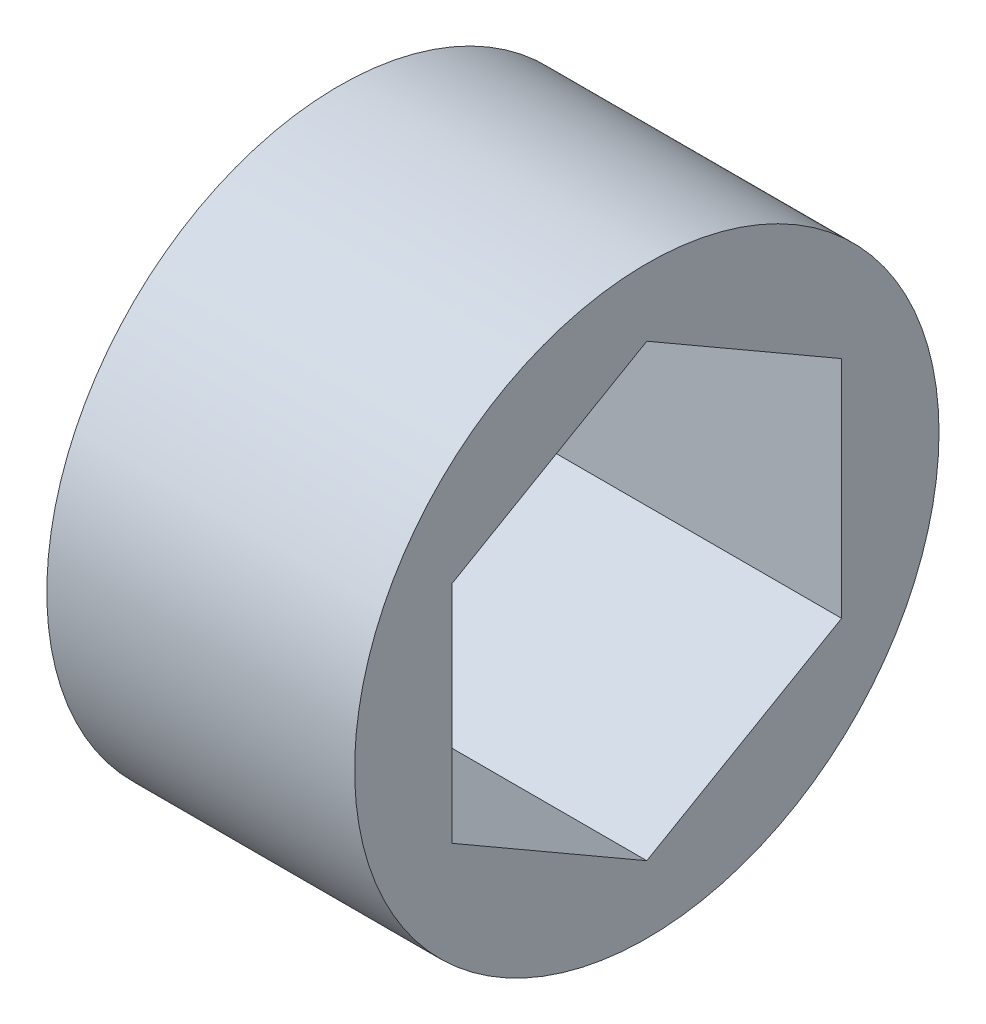
SolidWorks part; units mm, degrees
ref_plane "Front Plane" through (0, 0, 0) normal (0, 0, 1) x (1, 0, 0)
ref_plane "Top Plane" through (0, 0, 0) normal (0, 1, 0) x (1, 0, 0)
ref_plane "Right Plane" through (0, 0, 0) normal (1, 0, 0) x (0, 0, -1)
sketch "Sketch1" plane through (0, 0, 0) normal (1, 0, 0) x (0, 0, -1)
  line L1 (0, 7.3323) -> (-6.35, 3.6662)
  line L2 (-6.35, 3.6662) -> (-6.35, -3.6662)
  line L3 (-6.35, -3.6662) -> (0, -7.3323)
  line L4 (0, -7.3323) -> (6.35, -3.6662)
  line L5 (6.35, -3.6662) -> (6.35, 3.6662)
  line L6 (6.35, 3.6662) -> (0, 7.3323)
  circle A0 centre (0, 0) radius 9.525
  circle A1 centre (0, 0) radius 6.35 construction
  dimension "D2" = 19.05
  dimension "D1" = 12.7
extrude "Boss-Extrude1" add sketch "Sketch1" along normal blind 10.033
